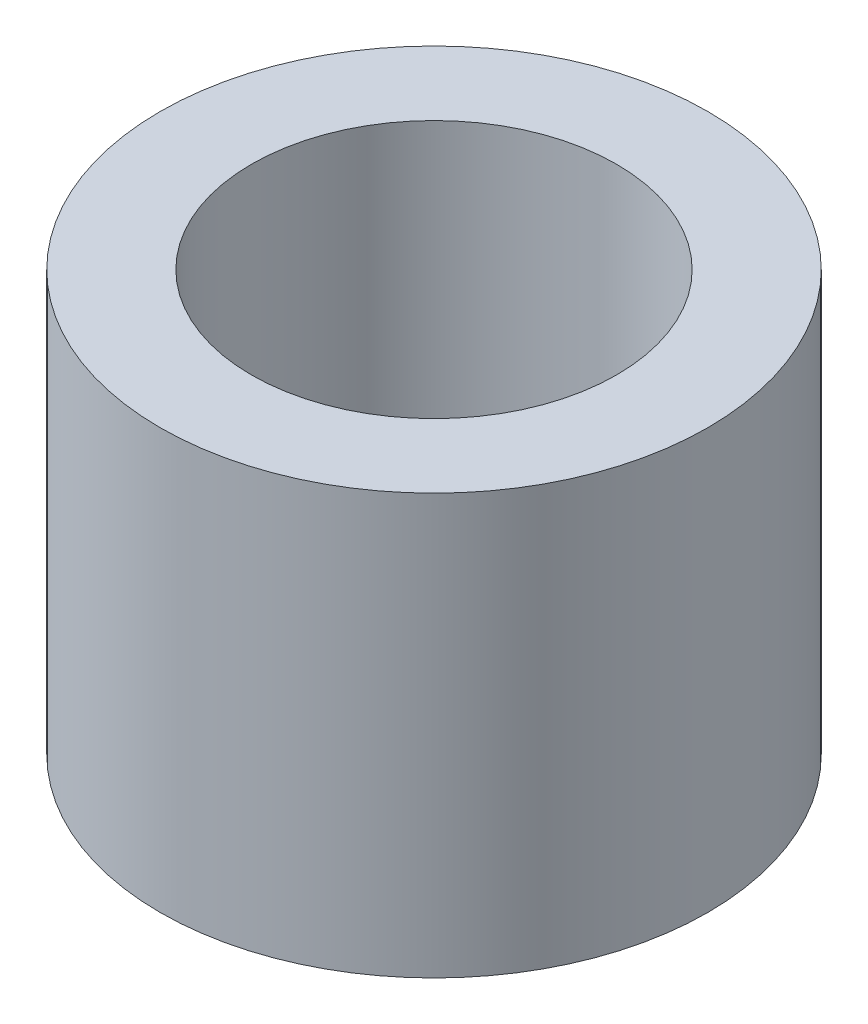
SolidWorks part; units mm, degrees
material "Pure Gold"
ref_plane "Front Plane" through (0, 0, 0) normal (0, 0, 1) x (1, 0, 0)
ref_plane "Top Plane" through (0, 0, 0) normal (0, 1, 0) x (1, 0, 0)
ref_plane "Right Plane" through (0, 0, 0) normal (1, 0, 0) x (0, 0, -1)
sketch "Sketch1" plane through (0, 0, 0) normal (0, 1, 0) x (1, 0, 0)
  circle A0 centre (0, 0) radius 0.5
  circle A1 centre (0, 0) radius 0.75
  dimension "D1" = 1
  dimension "D2" = 1.5
extrude "Extrude1" add sketch "Sketch1" along normal mid plane 1.15
